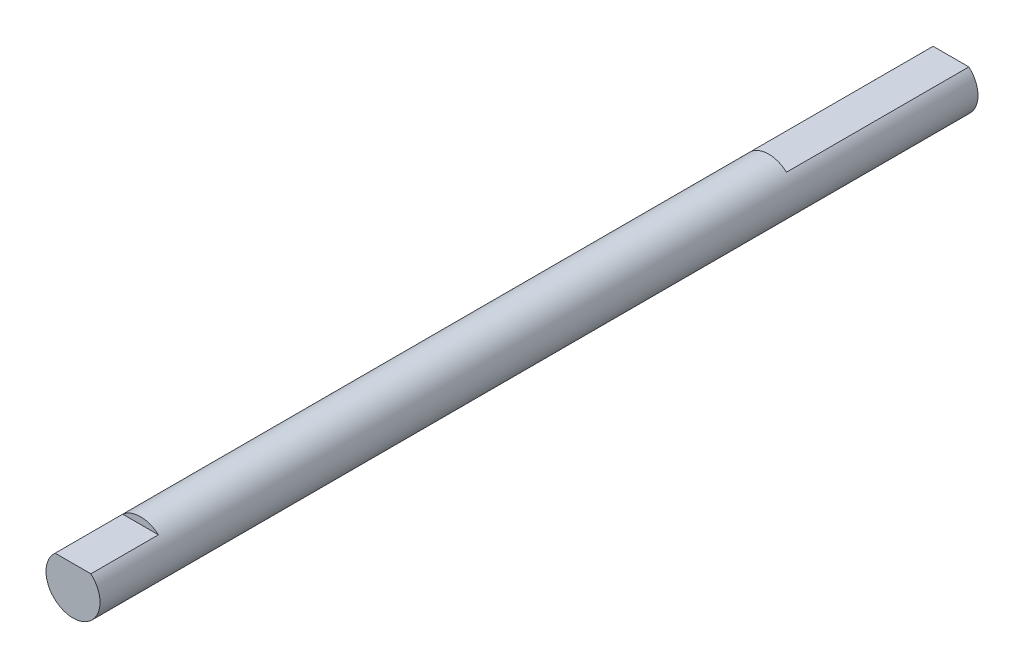
SolidWorks part; units mm, degrees
ref_plane "Plano frontal" through (0, 0, 0) normal (0, 0, 1) x (1, 0, 0)
ref_plane "Plano superior" through (0, 0, 0) normal (0, 1, 0) x (1, 0, 0)
ref_plane "Plano direito" through (0, 0, 0) normal (1, 0, 0) x (0, 0, -1)
sketch "Esboço1" plane through (0, 0, 0) normal (0, 0, 1) x (1, 0, 0)
  circle A0 centre (0, 0) radius 4
  dimension "D1" = 8
extrude "Ressalto-extrusão1" add sketch "Esboço1" along normal blind 72 and the other way blind 58
sketch "Esboço2" plane through (0, 0, 72) normal (0, 0, 1) x (1, 0, 0)
  line L0 (0, 4) -> (0, 3) construction
  line L1 (2.6458, 3) -> (-2.6458, 3)
  circle A0 centre (0, 0) radius 4 construction
  arc A1 (2.6458, 3) -> (-2.6458, 3) centre (0, 0) ccw
  dimension "D1" = 1
extrude "Corte-extrusão1" cut sketch "Esboço2" against normal blind 10
sketch "Esboço6" plane through (0, 0, -58) normal (0, 0, -1) x (-1, 0, 0)
  line L0 (0, 4) -> (0, 3) construction
  line L2 (2.6458, 3) -> (-2.6458, 3)
  circle A0 centre (0, 0) radius 4 construction
  arc A1 (2.6458, 3) -> (-2.6458, 3) centre (0, 0) ccw
  dimension "D1" = 1
extrude "Corte-extrusão2" cut sketch "Esboço6" against normal blind 27
